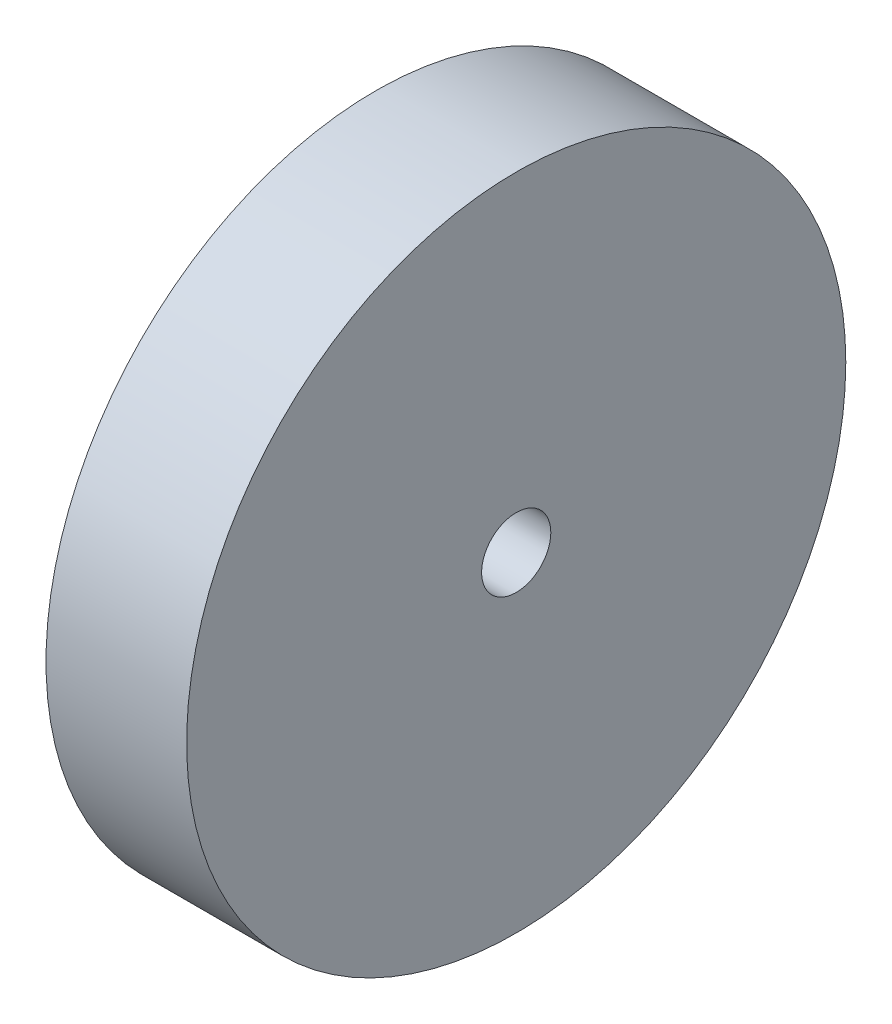
SolidWorks part; units mm, degrees
ref_plane "Front Plane" through (0, 0, 0) normal (0, 0, 1) x (1, 0, 0)
ref_plane "Top Plane" through (0, 0, 0) normal (0, 1, 0) x (1, 0, 0)
ref_plane "Right Plane" through (0, 0, 0) normal (1, 0, 0) x (0, 0, -1)
other "Bounding Box"
ref_plane "Default Plane" through (13.8565, 3.175, 6.7999) normal (0, -1, 0) x (-1, 0, 0)
sketch "Sketch1" plane through (0, 0, 0) normal (1, 0, 0) x (0, 0, -1)
  circle A0 centre (0, 0) radius 23.8125
  circle A1 centre (0, 0) radius 2.5
  dimension "D1" = 47.625
  dimension "D2" = 5
extrude "Boss-Extrude1" add sketch "Sketch1" along normal mid plane 10.16
